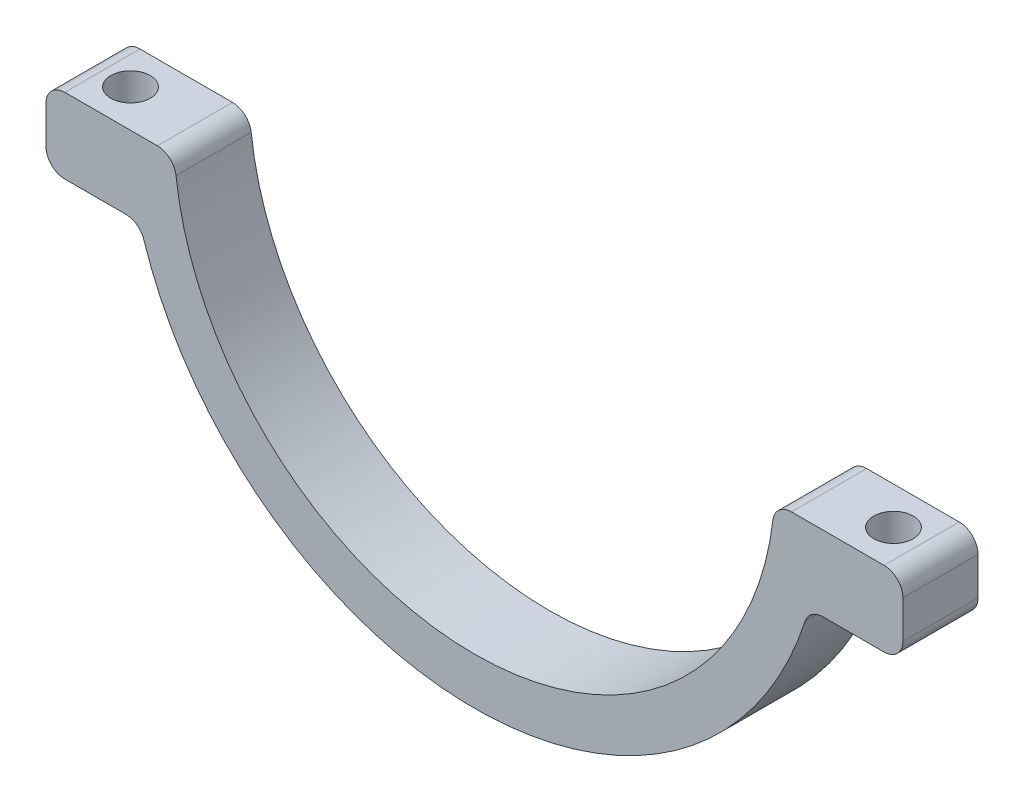
SolidWorks part; units mm, degrees
ref_plane "Front Plane" through (0, 0, 0) normal (0, 0, 1) x (1, 0, 0)
ref_plane "Top Plane" through (0, 0, 0) normal (0, 1, 0) x (1, 0, 0)
ref_plane "Right Plane" through (0, 0, 0) normal (1, 0, 0) x (0, 0, -1)
sketch "Sketch2" plane through (0, 0, 0) normal (0, 0, 1) x (1, 0, 0)
  circle A0 centre (0, 0) radius 31.7 construction
  dimension "D1" = 63.4
sketch "Sketch3" plane through (0, 0, 0) normal (0, 0, 1) x (1, 0, 0)
  line L0 (-31.9374, -2) -> (-45.623, -2)
  line L1 (31.9374, -2) -> (45.623, -2)
  line L11 (35.623, -10) -> (45.623, -10)
  line L12 (45.623, -10) -> (45.623, -2)
  line L13 (-35.623, -10) -> (-45.623, -10)
  line L14 (-45.623, -10) -> (-45.623, -2)
  line L15 (40.623, -10) -> (40.623, -2) construction
  line L16 (37.623, -6) -> (43.623, -6) construction
  arc A2 (31.9374, -2) -> (-31.9374, -2) centre (0, 0) cw
  circle A3 centre (0, 0) radius 31.7 construction
  arc A8 (-35.623, -10) -> (35.623, -10) centre (0, 0) ccw
  point P24 (40.623, -6)
  dimension "D1" = 0.3
  dimension "D7" = 5
  dimension "D8" = 8
  dimension "D9" = 6
  dimension "D10" = 2
  dimension "D11" = 2
  dimension "D12" = 2
extrude "Boss-Extrude1" add sketch "Sketch3" along normal blind 8
sketch "Sketch5" plane through (0, -2, 0) normal (0, -1, 0) x (1, 0, 0)
  line L0 (37.623, 0) -> (43.623, 0) construction
  line L1 (37.623, 0) -> (43.623, 0) construction
  line L2 (40.623, 0) -> (40.623, 8) construction
  line L3 (45.623, 8) -> (31.9374, 8) construction
  line L4 (0, 0) -> (0, 8) construction
  line L5 (31.7, 0) -> (-31.7, 0) construction
  line L6 (31.9374, 8) -> (-31.9374, 8) construction
  circle A0 centre (40.623, 4) radius 2.1
  dimension "D1" = 4.2
extrude "Cut-Extrude1" cut sketch "Sketch5" along normal blind 5
sketch "Sketch6" plane through (0, -2, 0) normal (0, 1, 0) x (1, 0, 0)
  circle A0 centre (40.623, -4) radius 1.65
  dimension "D1" = 3.3
extrude "Cut-Extrude2" cut sketch "Sketch6" against normal through all
mirror "Mirror1" about plane through (0, 0, 0) normal (1, 0, 0) of "Cut-Extrude2", "Cut-Extrude1"
fillet "Fillet1" radius 2 8 edges at (-31.9374, -2, 4) (31.9374, -2, 4) (35.623, -10, 4) (-35.623, -10, 4) (-45.623, -10, 4) (-45.623, -2, 4) (45.623, -10, 4) (45.623, -2, 4)
